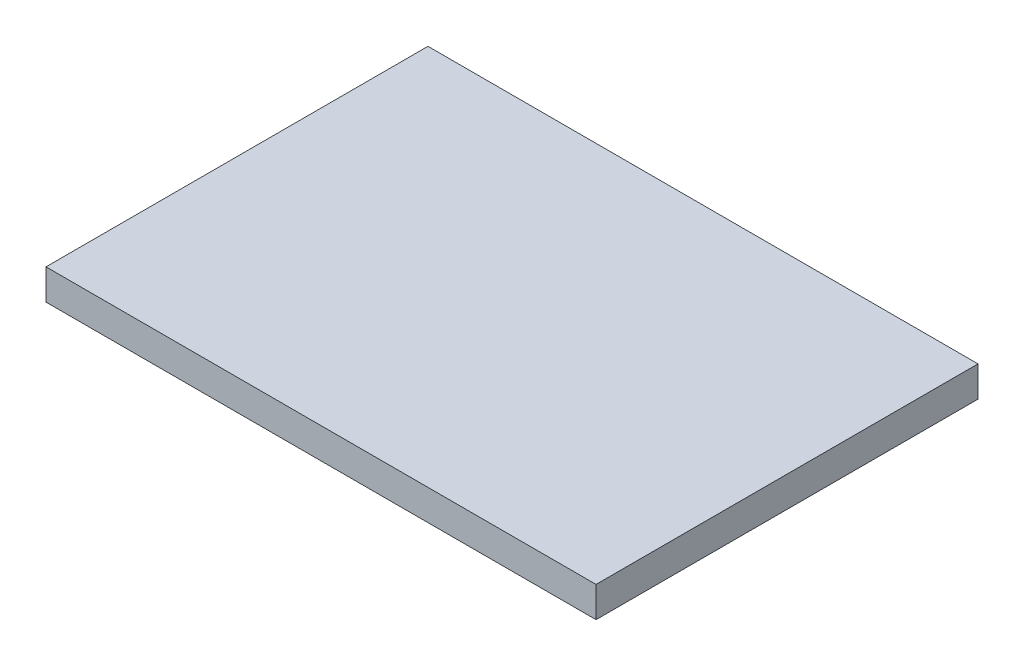
SolidWorks part; units mm, degrees
ref_plane "前视基准面" through (0, 0, 0) normal (0, 0, 1) x (1, 0, 0)
ref_plane "上视基准面" through (0, 0, 0) normal (0, 1, 0) x (1, 0, 0)
ref_plane "右视基准面" through (0, 0, 0) normal (1, 0, 0) x (0, 0, -1)
sketch "草图1" plane through (0, 0, 0) normal (0, 1, 0) x (1, 0, 0)
  line L1 (-18, 12.5) -> (18, 12.5)
  line L2 (-18, 12.5) -> (-18, -12.5)
  line L3 (-18, -12.5) -> (18, -12.5)
  line L4 (18, 12.5) -> (18, -12.5)
  line L5 (-18, 12.5) -> (18, -12.5) construction
  line L6 (-18, -12.5) -> (18, 12.5) construction
  point P0 (0, 0)
  dimension "D1" = 25
  dimension "D2" = 36
extrude "凸台-拉伸1" add sketch "草图1" along normal blind 2
